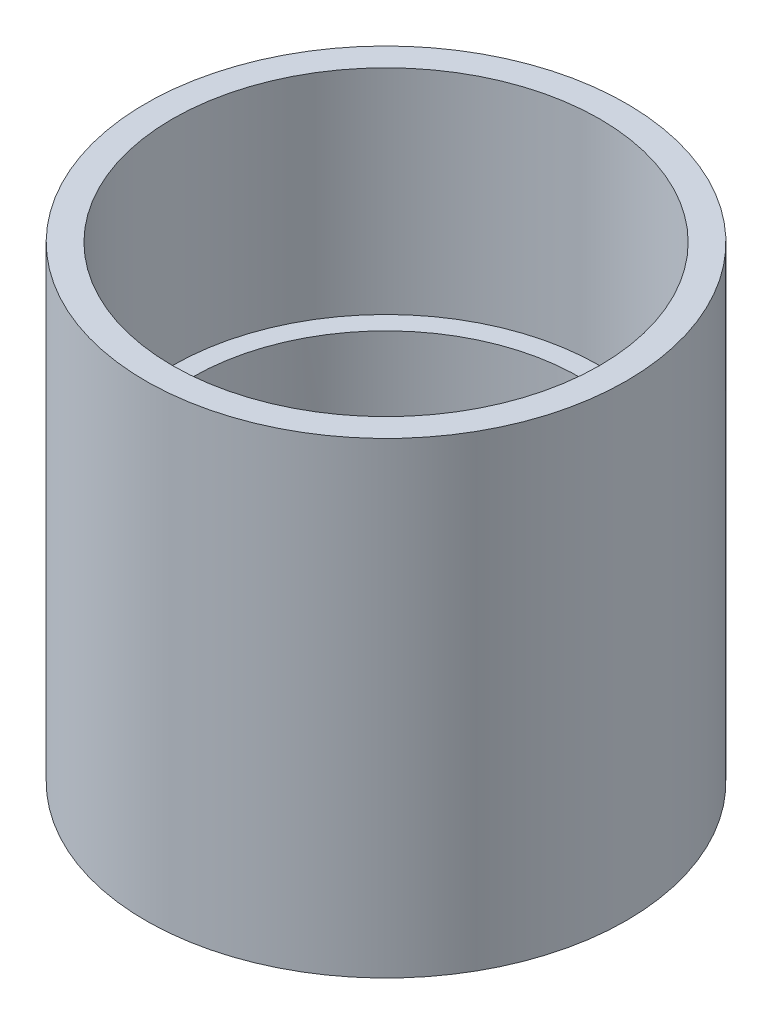
SolidWorks part; units mm, degrees
material "AISI 321 Annealed Stainless Steel (SS)"
ref_plane "Front Plane" through (0, 0, 0) normal (0, 0, 1) x (1, 0, 0)
ref_plane "Top Plane" through (0, 0, 0) normal (0, 1, 0) x (1, 0, 0)
ref_plane "Right Plane" through (0, 0, 0) normal (1, 0, 0) x (0, 0, -1)
sketch "Sketch1" plane through (0, 0, 0) normal (0, 0, 1) x (1, 0, 0)
  line L0 (0, -1459.8926) -> (0, 71534.7381) construction
  line L1 (16, -17.5) -> (16, -4.5)
  line L2 (16, -4.5) -> (14.5, -4.5)
  line L5 (14.5, -4.5) -> (14.5, 17.5)
  line L6 (14.5, 17.5) -> (18, 17.5)
  line L7 (18, 17.5) -> (18, -17.5)
  line L8 (18, -17.5) -> (16, -17.5)
  point P12 (18, 0)
  dimension "D1" = 35
  dimension "D2" = 36
  dimension "D3" = 32
  dimension "D4" = 22
  dimension "D5" = 29
revolve "Revolve1" add sketch "Sketch1" angle 360 about L0
sketch "Sketch2" plane through (0, 17.5, 0) normal (0, 1, 0) x (1, 0, 0)
  circle A0 centre (0, 0) radius 16 construction
  circle A1 centre (0, 0) radius 16
extrude "Cut-Extrude1" cut sketch "Sketch2" against normal blind 16
